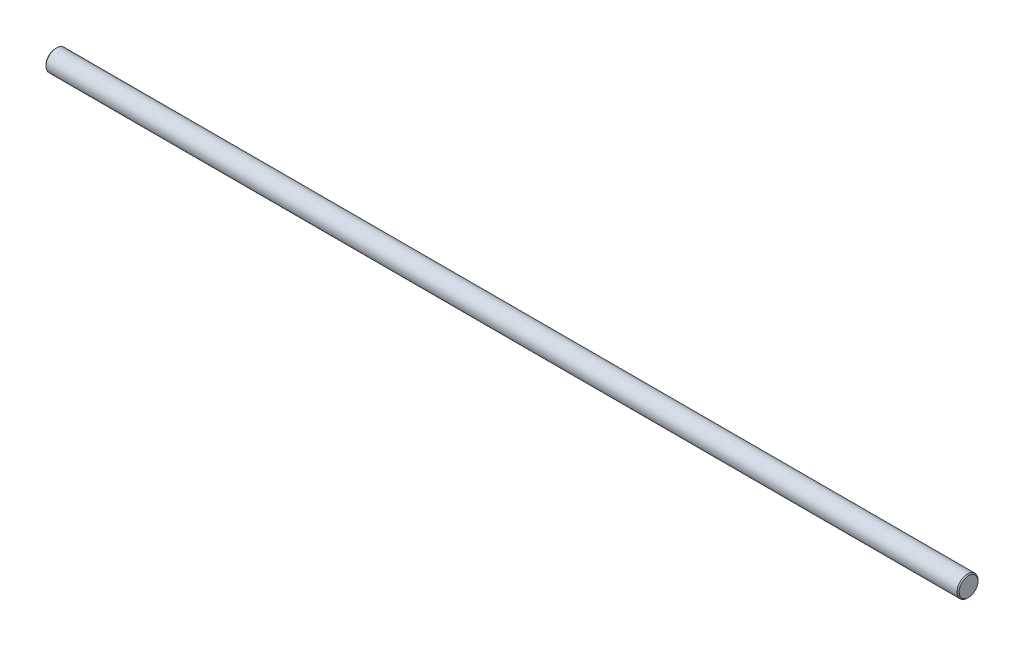
SolidWorks part; units mm, degrees
ref_plane "Front Plane" through (0, 0, 0) normal (0, 0, 1) x (1, 0, 0)
ref_plane "Top Plane" through (0, 0, 0) normal (0, 1, 0) x (1, 0, 0)
ref_plane "Right Plane" through (0, 0, 0) normal (1, 0, 0) x (0, 0, -1)
ref_plane "Plane1" through (0, 0, 0) normal (0, 0, 1) x (1, 0, 0)
sketch "Sketch1" plane through (0, 0, 0) normal (0, 0, 1) x (1, 0, 0)
  line L0 (0, 0) -> (0, 4.5)
  line L1 (0, 4.5) -> (0.5, 5)
  line L2 (0.5, 5) -> (434.5, 5)
  line L3 (434.5, 5) -> (435, 4.5)
  line L4 (435, 4.5) -> (435, 0)
  line L5 (435, 0) -> (0, 0)
  line L6 (435, 0) -> (0, 0) construction
  dimension "D1" = 435
  dimension "D2" = 5
  dimension "D3" = 4.5
  dimension "D4" = 0.5
  dimension "D5" = 4.5
  dimension "D6" = 0.5
revolve "Revolve1" add sketch "Sketch1" angle 360 about L6
